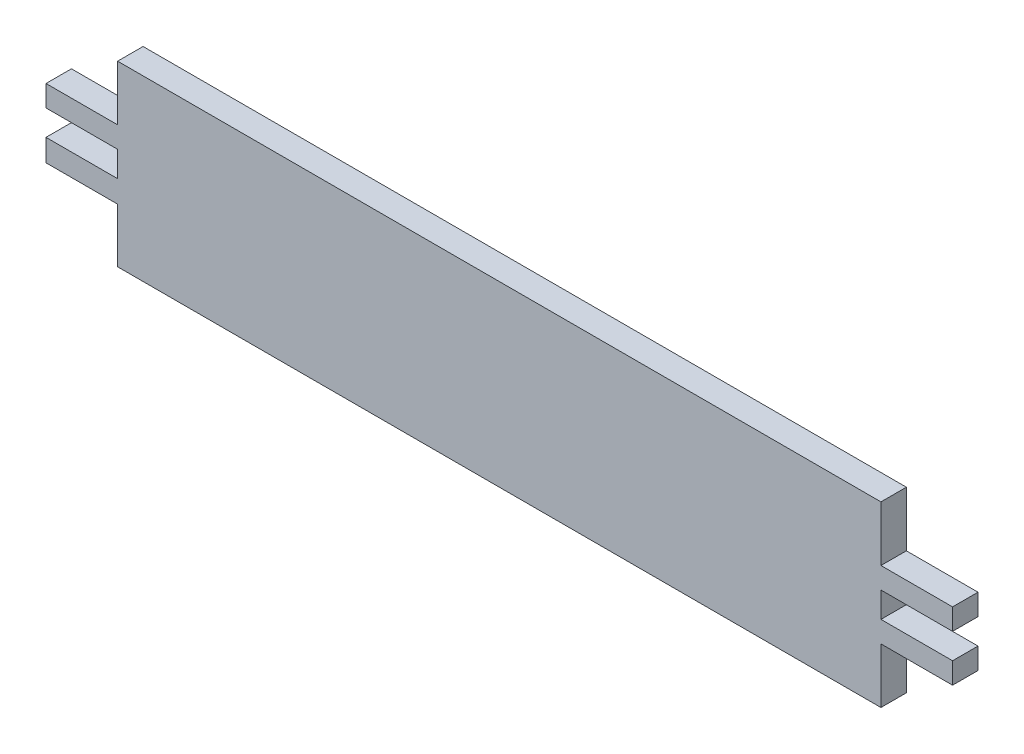
SolidWorks part; units mm, degrees
ref_plane "Front Plane" through (0, 0, 0) normal (0, 0, 1) x (1, 0, 0)
ref_plane "Top Plane" through (0, 0, 0) normal (0, 1, 0) x (1, 0, 0)
ref_plane "Right Plane" through (0, 0, 0) normal (1, 0, 0) x (0, 0, -1)
sketch "Sketch3" plane through (0, 0, 0) normal (0, 0, 1) x (1, 0, 0)
  line L0 (-59.9171, 29.2045) -> (120.0829, 29.2045)
  line L1 (120.0829, 29.2045) -> (120.0829, 16.2045)
  line L2 (120.0829, 16.2045) -> (136.973, 16.2045)
  line L3 (136.973, 16.2045) -> (136.973, 11.2045)
  line L4 (136.973, 11.2045) -> (120.0829, 11.2045)
  line L6 (120.0829, -12.7955) -> (120.0829, 0.2045)
  line L7 (120.0829, 0.2045) -> (136.973, 0.2045)
  line L8 (136.973, 0.2045) -> (136.973, 5.2045)
  line L9 (136.973, 5.2045) -> (120.0829, 5.2045)
  line L10 (120.0829, 5.2045) -> (120.0829, 11.2045)
  line L11 (120.0829, -12.7955) -> (-59.9171, -12.7955)
  line L12 (-59.9171, -12.7955) -> (-59.9171, 0)
  line L13 (-59.9171, 0) -> (-76.8071, 0)
  line L14 (-76.8071, 0) -> (-76.8071, 5.2045)
  line L15 (-76.8071, 5.2045) -> (-59.9171, 5.2045)
  line L16 (-59.9171, 5.2045) -> (-59.9171, 11.2045)
  line L17 (-59.9171, 11.2045) -> (-76.8071, 11.2045)
  line L18 (-76.8071, 11.2045) -> (-76.8071, 16.2045)
  line L19 (-76.8071, 16.2045) -> (-59.9171, 16.2045)
  line L20 (-59.9171, 16.2045) -> (-59.9171, 29.2045)
extrude "Boss-Extrude1" add sketch "Sketch3" along normal blind 6
